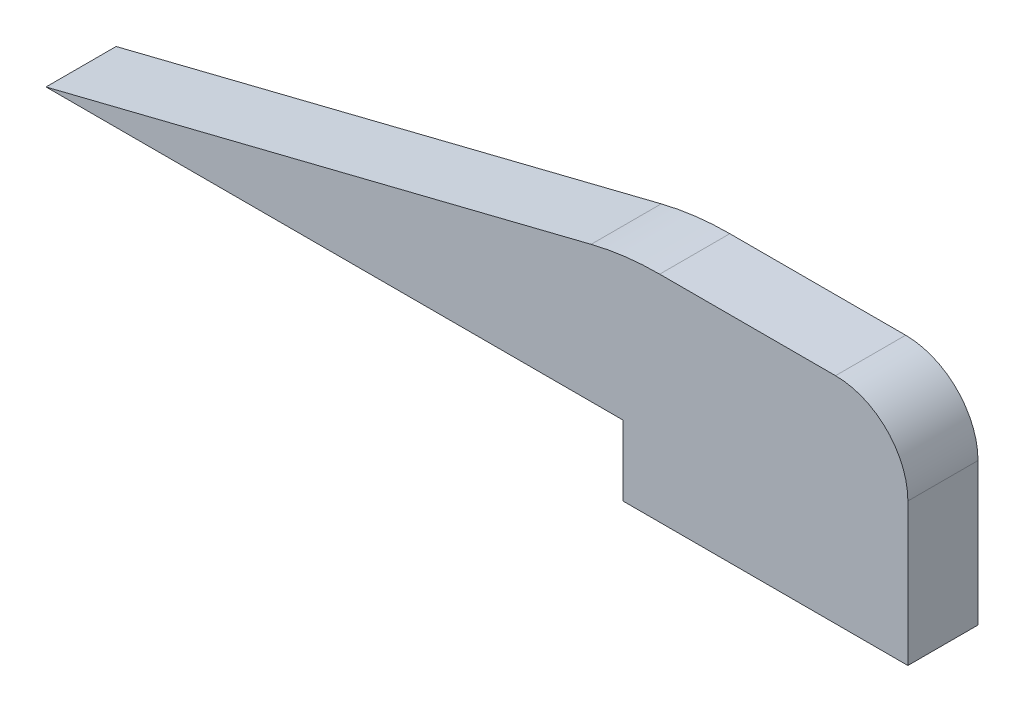
SolidWorks part; units mm, degrees
ref_plane "Front Plane" through (0, 0, 0) normal (0, 0, 1) x (1, 0, 0)
ref_plane "Top Plane" through (0, 0, 0) normal (0, 1, 0) x (1, 0, 0)
ref_plane "Right Plane" through (0, 0, 0) normal (1, 0, 0) x (0, 0, -1)
sketch "Sketch1" plane through (0, 0, 0) normal (0, 0, 1) x (1, 0, 0)
  line L0 (0, 0) -> (23.8832, 5.9708) construction
  line L1 (26.9634, 6.35) -> (34.925, 6.35) construction
  line L4 (38.1, -3.175) -> (25.4, -3.175) construction
  line L5 (25.4, -3.175) -> (25.4, 0) construction
  line L6 (25.4, 0) -> (0, 0) construction
  line L7 (38.1, 3.175) -> (38.1, -3.175) construction
  line L8 (38.2016, 3.175) -> (38.2016, -3.2766)
  line L9 (38.2016, -3.2766) -> (25.2984, -3.2766)
  line L10 (25.2984, -3.2766) -> (25.2984, -0.1016)
  line L11 (25.2984, -0.1016) -> (-0.8253, -0.1016)
  line L12 (-0.8253, -0.1016) -> (23.8586, 6.0694)
  line L13 (26.9634, 6.4516) -> (34.925, 6.4516)
  arc A0 (23.8832, 5.9708) -> (26.9634, 6.35) centre (26.9634, -6.35) cw construction
  arc A2 (34.925, 6.35) -> (38.1, 3.175) centre (34.925, 3.175) cw construction
  arc A3 (23.8586, 6.0694) -> (26.9634, 6.4516) centre (26.9634, -6.35) cw
  arc A4 (34.925, 6.4516) -> (38.2016, 3.175) centre (34.925, 3.175) cw
  point P11 (25.4, 6.35)
  dimension "D1" = 12.7
  dimension "D2" = 3.175
  dimension "D6" = 3.175
  dimension "D3" = 25.4
  dimension "D4" = 6.35
  dimension "D5" = 12.7
  dimension "D7" = 0.1016
extrude "Boss-Extrude1" add sketch "Sketch1" along normal blind 3.175
